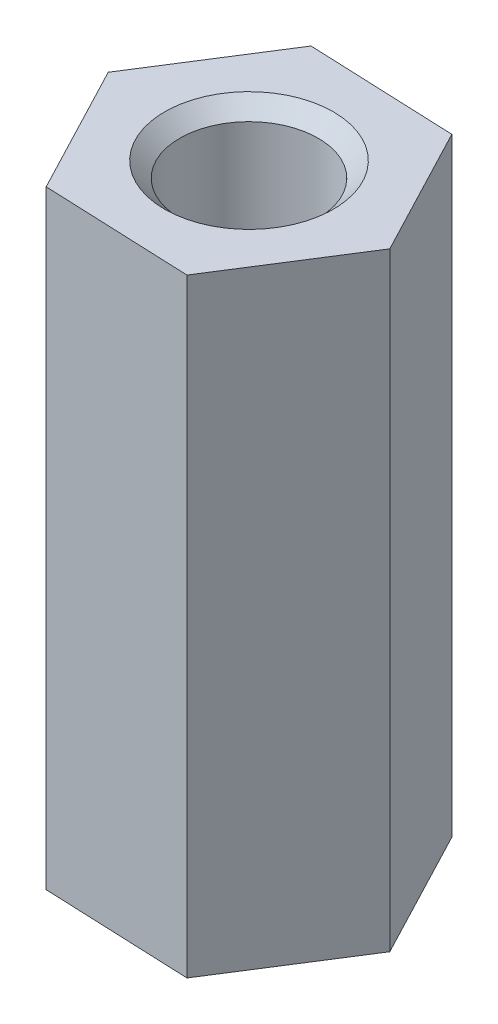
SolidWorks part; units mm, degrees
ref_plane "前视基准面" through (0, 0, 0) normal (0, 0, 1) x (1, 0, 0)
ref_plane "上视基准面" through (0, 0, 0) normal (0, 1, 0) x (1, 0, 0)
ref_plane "右视基准面" through (0, 0, 0) normal (1, 0, 0) x (0, 0, -1)
sketch "草图1" plane through (0, 0, 0) normal (0, 1, 0) x (1, 0, 0)
  line L1 (1.2317, -2.3529) -> (2.6535, -0.1098)
  line L2 (2.6535, -0.1098) -> (1.4218, 2.2432)
  line L3 (1.4218, 2.2432) -> (-1.2317, 2.3529)
  line L4 (-1.2317, 2.3529) -> (-2.6535, 0.1098)
  line L5 (-2.6535, 0.1098) -> (-1.4218, -2.2432)
  line L6 (-1.4218, -2.2432) -> (1.2317, -2.3529)
  circle A0 centre (0, 0) radius 2.3 construction
  circle A1 centre (0, 0) radius 1.1
  dimension "D2" = 2.2
  dimension "D1" = 4.6
extrude "凸台-拉伸1" add sketch "草图1" along normal blind 11
hole_wizard "M3 螺纹孔2" positions "草图2" profile "草图3" tap size "M3" standard "GB" end condition through all
sketch "草图2" plane through (0, 11, 0) normal (0, 1, 0) x (1, 0, 0)
  point P0 (0, 0)
sketch "草图3" plane through (0, 11, 0) normal (1, 0, 0) x (0, 0, 1)
  line L0 (0, 0) -> (0, 11)
  line L1 (0, 11) -> (1.25, 11)
  line L2 (1.25, 11) -> (1.25, 0.275)
  line L3 (1.25, 0.275) -> (1.525, 0)
  line L5 (1.525, 0) -> (0, 0)
  line L6 (-1.25, 0.275) -> (-1.525, 0) construction
  line L11 (0, -6.35) -> (0, 107.95) construction
  dimension "通孔螺纹孔钻头直径" = 2.5
  dimension "通孔螺纹孔钻头深度" = 11
  dimension "近端锥形沉头孔直径" = 3.05
  dimension "近端锥形沉头孔角度" = 90
cosmetic thread "孔螺蚊线2" parameters "D2"=3
